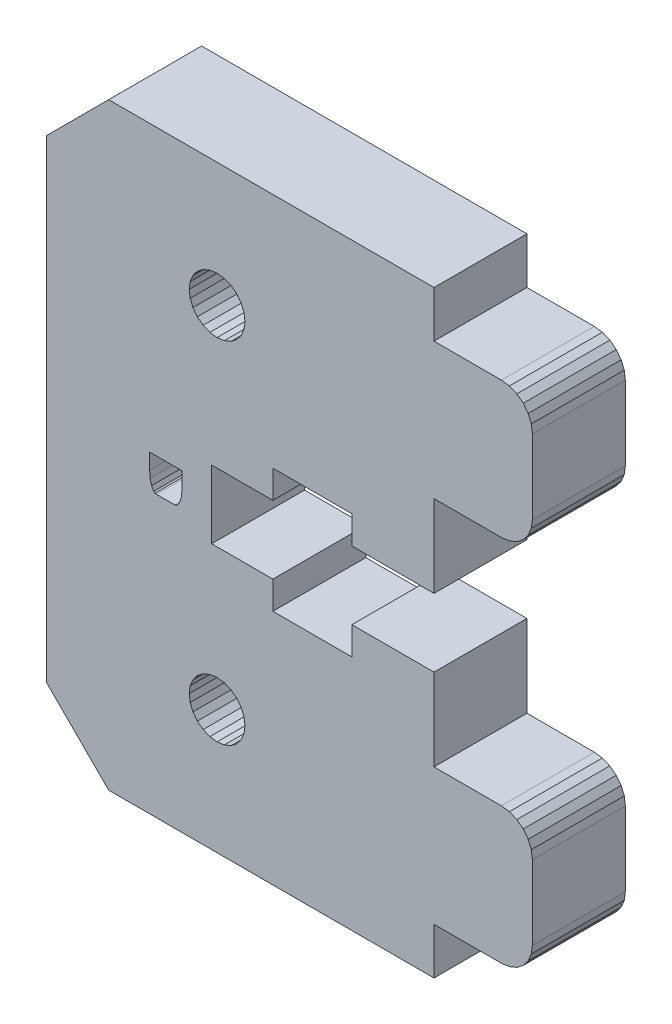
SolidWorks part; units mm, degrees
material "Maple"
ref_plane "Front Plane" through (0, 0, 0) normal (0, 0, 1) x (1, 0, 0)
ref_plane "Top Plane" through (0, 0, 0) normal (0, 1, 0) x (1, 0, 0)
ref_plane "Right Plane" through (0, 0, 0) normal (1, 0, 0) x (0, 0, -1)
sketch "Sketch1" plane through (0, 0, 0) normal (0, 0, 1) x (1, 0, 0)
  line L7334 (294.9322, 259.4506) -> (295.2182, 259.0778)
  line L7335 (295.2182, 259.0778) -> (295.591, 258.7917)
  line L7336 (295.591, 258.7917) -> (296.0252, 258.6119)
  line L7337 (296.0252, 258.6119) -> (296.491, 258.5506)
  line L7338 (296.491, 258.5506) -> (296.9569, 258.6119)
  line L7339 (296.9569, 258.6119) -> (297.391, 258.7917)
  line L7340 (297.391, 258.7917) -> (297.7638, 259.0778)
  line L7341 (297.7638, 259.0778) -> (298.0499, 259.4506)
  line L7342 (298.0499, 259.4506) -> (298.2297, 259.8847)
  line L7343 (298.2297, 259.8847) -> (298.291, 260.3506)
  line L7344 (315.841, 241.2826) -> (316.2552, 240.9648)
  line L7345 (315.3587, 241.4824) -> (315.841, 241.2826)
  line L7346 (310.491, 241.5506) -> (314.841, 241.5506)
  line L7347 (316.2552, 257.1364) -> (316.5731, 257.5506)
  line L7348 (300.091, 245.0506) -> (305.191, 245.0506)
  line L7349 (305.191, 245.0506) -> (305.191, 246.8506)
  line L7350 (310.491, 251.2506) -> (305.191, 251.2506)
  line L7351 (316.841, 239.5506) -> (316.841, 234.7506)
  line L7352 (300.091, 251.2506) -> (296.141, 251.2506)
  line L7353 (316.2552, 233.3364) -> (316.5731, 233.7506)
  line L7354 (300.091, 246.8506) -> (300.091, 245.0506)
  line L7355 (310.491, 246.8506) -> (310.491, 241.5506)
  line L7356 (316.5731, 233.7506) -> (316.7729, 234.233)
  line L7357 (315.841, 265.0826) -> (316.2552, 264.7648)
  line L7358 (315.841, 233.0185) -> (316.2552, 233.3364)
  line L7359 (316.7729, 258.0329) -> (316.841, 258.5506)
  line L7360 (316.841, 263.3506) -> (316.841, 258.5506)
  line L7361 (316.7729, 263.8682) -> (316.841, 263.3506)
  line L7362 (314.841, 265.3506) -> (315.3587, 265.2824)
  line L7363 (316.7729, 240.0682) -> (316.841, 239.5506)
  line L7364 (314.841, 232.7506) -> (315.3587, 232.8187)
  line L7365 (315.3587, 232.8187) -> (315.841, 233.0185)
  line L7366 (305.191, 251.2506) -> (305.191, 253.0506)
  line L7367 (315.3587, 265.2824) -> (315.841, 265.0826)
  line L7368 (300.091, 253.0506) -> (300.091, 251.2506)
  line L7369 (296.141, 246.8506) -> (300.091, 246.8506)
  line L7370 (310.491, 232.7506) -> (310.491, 229.7506)
  line L7371 (310.491, 229.7506) -> (289.491, 229.7506)
  line L7372 (310.491, 265.3506) -> (310.491, 268.3506)
  line L7373 (310.491, 268.3506) -> (289.491, 268.3506)
  line L7374 (316.5731, 257.5506) -> (316.7729, 258.0329)
  line L7375 (314.841, 232.7506) -> (310.491, 232.7506)
  line L7376 (316.2552, 264.7648) -> (316.5731, 264.3506)
  line L7377 (315.841, 256.8185) -> (316.2552, 257.1364)
  line L7378 (296.141, 251.2506) -> (296.141, 246.8506)
  line L7379 (305.191, 253.0506) -> (300.091, 253.0506)
  line L7380 (316.7729, 234.233) -> (316.841, 234.7506)
  line L7381 (305.191, 246.8506) -> (310.491, 246.8506)
  line L7382 (310.491, 256.5506) -> (310.491, 251.2506)
  line L7383 (314.841, 241.5506) -> (315.3587, 241.4824)
  line L7384 (314.841, 256.5506) -> (310.491, 256.5506)
  line L7385 (314.841, 256.5506) -> (315.3587, 256.6187)
  line L7386 (316.5731, 264.3506) -> (316.7729, 263.8682)
  line L7387 (315.3587, 256.6187) -> (315.841, 256.8185)
  line L7388 (310.491, 265.3506) -> (314.841, 265.3506)
  line L7389 (316.2552, 240.9648) -> (316.5731, 240.5506)
  line L7390 (316.5731, 240.5506) -> (316.7729, 240.0682)
  line L7391 (296.0252, 236.0119) -> (296.491, 235.9506)
  line L7392 (296.491, 235.9506) -> (296.9569, 236.0119)
  line L7393 (296.9569, 236.0119) -> (297.391, 236.1917)
  line L7394 (297.391, 236.1917) -> (297.7638, 236.4778)
  line L7395 (297.7638, 236.4778) -> (298.0499, 236.8506)
  line L7396 (298.0499, 236.8506) -> (298.2297, 237.2847)
  line L7397 (298.2297, 237.2847) -> (298.291, 237.7506)
  line L7398 (298.291, 260.3506) -> (298.2297, 260.8165)
  line L7399 (298.2297, 260.8165) -> (298.0499, 261.2506)
  line L7400 (298.0499, 261.2506) -> (297.7638, 261.6234)
  line L7401 (297.7638, 261.6234) -> (297.391, 261.9094)
  line L7402 (297.391, 261.9094) -> (296.9569, 262.0892)
  line L7403 (296.9569, 262.0892) -> (296.491, 262.1506)
  line L7404 (296.491, 262.1506) -> (296.0252, 262.0892)
  line L7405 (296.0252, 262.0892) -> (295.591, 261.9094)
  line L7406 (295.591, 261.9094) -> (295.2182, 261.6234)
  line L7407 (295.2182, 261.6234) -> (294.9322, 261.2506)
  line L7408 (294.9322, 261.2506) -> (294.7524, 260.8165)
  line L7409 (294.7524, 260.8165) -> (294.691, 260.3506)
  line L7410 (294.691, 260.3506) -> (294.7524, 259.8847)
  line L7411 (294.7524, 259.8847) -> (294.9322, 259.4506)
  line L7412 (285.491, 233.7506) -> (289.491, 229.7506)
  line L7413 (285.491, 264.3506) -> (285.491, 233.7506)
  line L7414 (285.491, 264.3506) -> (289.491, 268.3506)
  line L7415 (298.291, 237.7506) -> (298.2297, 238.2165)
  line L7416 (298.2297, 238.2165) -> (298.0499, 238.6506)
  line L7417 (298.0499, 238.6506) -> (297.7638, 239.0234)
  line L7418 (297.7638, 239.0234) -> (297.391, 239.3094)
  line L7419 (297.391, 239.3094) -> (296.9569, 239.4893)
  line L7420 (296.9569, 239.4893) -> (296.491, 239.5506)
  line L7421 (296.491, 239.5506) -> (296.0252, 239.4893)
  line L7422 (296.0252, 239.4893) -> (295.591, 239.3094)
  line L7423 (295.591, 239.3094) -> (295.2182, 239.0234)
  line L7424 (295.2182, 239.0234) -> (294.9322, 238.6506)
  line L7425 (294.9322, 238.6506) -> (294.7524, 238.2165)
  line L7426 (294.7524, 238.2165) -> (294.691, 237.7506)
  line L7427 (294.691, 237.7506) -> (294.7524, 237.2847)
  line L7428 (294.7524, 237.2847) -> (294.9322, 236.8506)
  line L7429 (294.9322, 236.8506) -> (295.2182, 236.4778)
  line L7430 (295.2182, 236.4778) -> (295.591, 236.1917)
  line L7431 (295.591, 236.1917) -> (296.0252, 236.0119)
  line L9639 (292.1369, 248.9549) -> (292.1673, 248.5217)
  line L9640 (292.1673, 248.5217) -> (292.2586, 248.1588)
  line L9641 (292.2586, 248.1588) -> (292.3999, 247.913)
  line L9642 (292.3999, 247.913) -> (292.4851, 247.8515)
  line L9643 (292.4851, 247.8515) -> (292.5802, 247.831)
  line L9644 (292.5802, 247.831) -> (293.7478, 247.831)
  line L9645 (293.7478, 247.831) -> (293.8439, 247.8515)
  line L9646 (293.8439, 247.8515) -> (293.9327, 247.913)
  line L9647 (293.9327, 247.913) -> (294.0881, 248.1588)
  line L9648 (294.0881, 248.1588) -> (294.1934, 248.5217)
  line L9649 (294.1934, 248.5217) -> (294.2286, 248.9549)
  line L9650 (294.2286, 248.9549) -> (294.2286, 249.9727)
  line L9651 (294.2286, 249.9727) -> (292.1369, 249.9727)
  line L9652 (292.1369, 249.9727) -> (292.1369, 248.9549)
  line L9653 (289.9206, 249.9727) -> (294.2286, 249.9727)
  line L9654 (294.2286, 249.9727) -> (294.2286, 248.9549)
  line L9655 (294.2286, 248.9549) -> (294.1934, 248.5217)
  line L9656 (294.1934, 248.5217) -> (294.0881, 248.1588)
  line L9657 (294.0881, 248.1588) -> (293.9328, 247.913)
  line L9658 (293.9328, 247.913) -> (293.844, 247.8515)
  line L9659 (293.844, 247.8515) -> (293.7478, 247.831)
  line L9660 (293.7478, 247.831) -> (292.5803, 247.831)
  line L9661 (292.5803, 247.831) -> (292.4853, 247.8515)
  line L9662 (292.4853, 247.8515) -> (292.4, 247.913)
  line L9663 (292.4, 247.913) -> (292.2588, 248.1588)
  line L9664 (292.2588, 248.1588) -> (292.1675, 248.5217)
  line L9665 (292.1675, 248.5217) -> (292.1371, 248.9549)
  line L9666 (292.1371, 248.9549) -> (292.1371, 249.9727)
  line L9667 (292.1371, 249.9727) -> (289.9206, 249.9727)
extrude "Boss-Extrude1" add sketch "Sketch1" along normal blind 6 contours L7414 L7413 L7412 L7371 L7370 L7375 L7364 L7365 L7358 L7353 L7356 L7380 L7351 L7363 L7390 L7389 L7344 L7345 L7383 L7346 L7355 L7381 L7349 L7348 L7354 L7369 L7378 L7352 L7368 L7379 L7366 L7350 L7382 L7384 L7385 L7387 L7377 L7347 L7374 L7359 L7360 L7361 L7386 L7376 L7357 L7367 L7362 L7388 L7372 L7373
